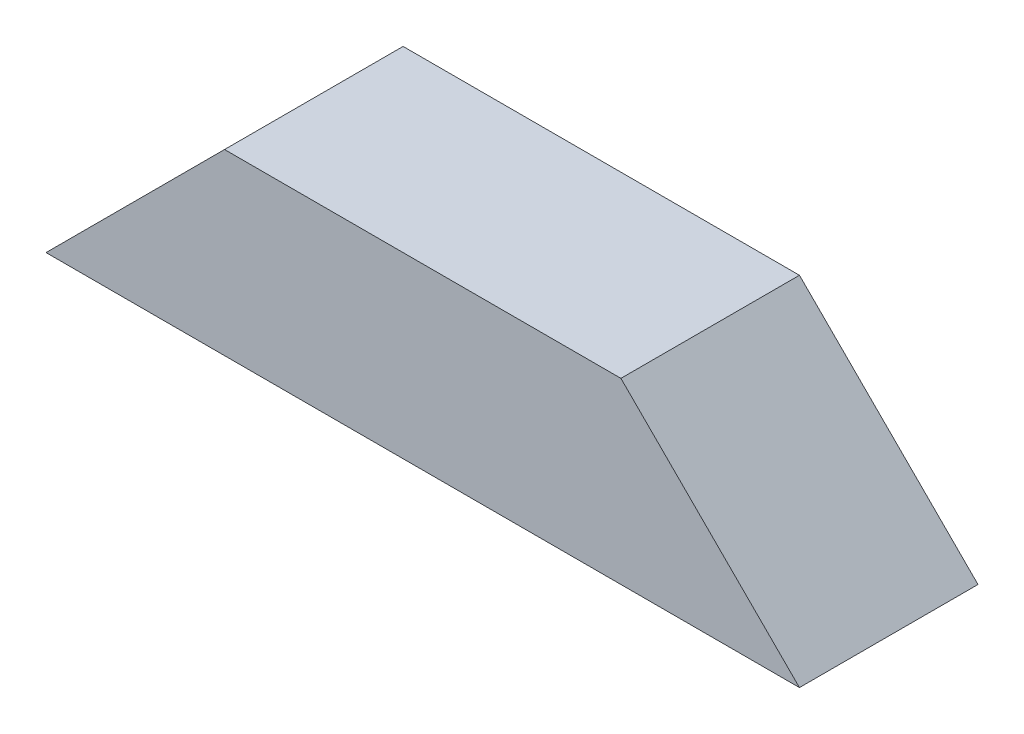
SolidWorks part; units mm, degrees
ref_plane "前视基准面" through (0, 0, 0) normal (0, 0, 1) x (1, 0, 0)
ref_plane "上视基准面" through (0, 0, 0) normal (0, 1, 0) x (1, 0, 0)
ref_plane "右视基准面" through (0, 0, 0) normal (1, 0, 0) x (0, 0, -1)
sketch "草图1" plane through (0, 0, 0) normal (0, 0, 1) x (1, 0, 0)
  line L0 (19.2218, 24.9611) -> (40.3218, 24.9611)
  line L1 (24.2218, 29.9611) -> (35.3218, 29.9611)
  line L2 (19.2218, 24.9611) -> (24.2218, 29.9611)
  line L3 (40.3218, 24.9611) -> (35.3218, 29.9611)
  dimension "D1" = 21.1
  dimension "D2" = 5
extrude "凸台-拉伸1" add sketch "草图1" along normal blind 5
